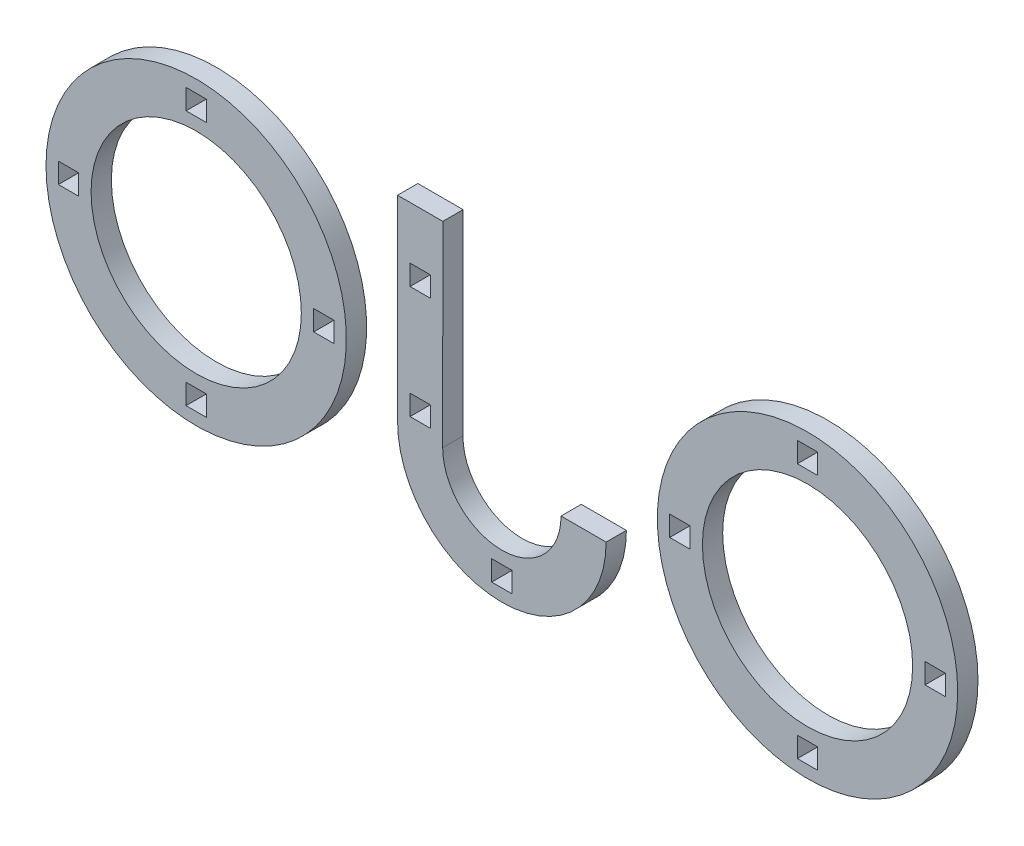
SolidWorks part; units mm, degrees
ref_plane "Ön Düzlem" through (0, 0, 0) normal (0, 0, 1) x (1, 0, 0)
ref_plane "Üst Düzlem" through (0, 0, 0) normal (0, 1, 0) x (1, 0, 0)
ref_plane "Sağ Düzlem" through (0, 0, 0) normal (1, 0, 0) x (0, 0, -1)
sketch "Sketch1" plane through (0, 0, 0) normal (0, 0, 1) x (1, 0, 0)
  line L17 (21.5127, -4.6025) -> (15.5066, -4.6025)
  line L50 (-0.2323, 21.5114) -> (-0.2534, -4.5961)
  line L51 (-6.2596, 21.5114) -> (-6.2596, -4.6025)
  line L52 (-0.2323, 21.5114) -> (-6.2596, 21.5114)
  line L53 (63.9821, 2.8614) -> (63.9821, 0.1614)
  line L54 (63.9821, 0.1614) -> (66.6821, 0.1614)
  line L59 (66.6821, 0.1614) -> (66.6821, 2.8614)
  line L60 (66.6821, 2.8614) -> (63.9821, 2.8614)
  line L61 (46.9821, 19.8614) -> (46.9821, 17.1614)
  line L62 (46.9821, 17.1614) -> (49.6821, 17.1614)
  line L63 (49.6821, 17.1614) -> (49.6821, 19.8614)
  line L64 (49.6821, 19.8614) -> (46.9821, 19.8614)
  line L65 (46.9821, -14.1386) -> (46.9821, -16.8386)
  line L66 (46.9821, -16.8386) -> (49.6821, -16.8386)
  line L67 (49.6821, -16.8386) -> (49.6821, -14.1386)
  line L68 (49.6821, -14.1386) -> (46.9821, -14.1386)
  line L69 (29.9821, 2.8614) -> (29.9821, 0.1614)
  line L70 (29.9821, 0.1614) -> (32.6821, 0.1614)
  line L71 (32.6821, 0.1614) -> (32.6821, 2.8614)
  line L72 (32.6821, 2.8614) -> (29.9821, 2.8614)
  line L73 (-17.4252, 2.8614) -> (-14.7252, 2.8614)
  line L74 (-4.5959, -0.4857) -> (-4.5959, -3.1857)
  line L75 (-17.4252, 0.1614) -> (-17.4252, 2.8614)
  line L76 (-14.7252, 0.1614) -> (-17.4252, 0.1614)
  line L77 (-14.7252, 2.8614) -> (-14.7252, 0.1614)
  line L78 (-34.4252, -14.1386) -> (-31.7252, -14.1386)
  line L79 (-34.4252, -16.8386) -> (-34.4252, -14.1386)
  line L80 (-31.7252, -16.8386) -> (-34.4252, -16.8386)
  line L81 (-31.7252, -14.1386) -> (-31.7252, -16.8386)
  line L82 (-34.4252, 19.8614) -> (-31.7252, 19.8614)
  line L83 (-34.4252, 17.1614) -> (-34.4252, 19.8614)
  line L84 (-31.7252, 17.1614) -> (-34.4252, 17.1614)
  line L85 (-31.7252, 19.8614) -> (-31.7252, 17.1614)
  line L86 (-51.4252, 2.8614) -> (-48.7252, 2.8614)
  line L87 (-51.4252, 0.1614) -> (-51.4252, 2.8614)
  line L88 (-48.7252, 0.1614) -> (-51.4252, 0.1614)
  line L89 (-48.7252, 2.8614) -> (-48.7252, 0.1614)
  line L90 (-4.5959, -3.1857) -> (-1.8959, -3.1857)
  line L91 (-4.5959, 14.5143) -> (-4.5959, 11.8143)
  line L92 (-4.5959, 11.8143) -> (-1.8959, 11.8143)
  line L93 (-1.8959, 11.8143) -> (-1.8959, 14.5143)
  line L94 (-1.8959, 14.5143) -> (-4.5959, 14.5143)
  line L95 (-1.8959, -3.1857) -> (-1.8959, -0.4857)
  line L96 (-1.8959, -0.4857) -> (-4.5959, -0.4857)
  line L98 (6.2766, -14.1355) -> (6.2766, -16.8355)
  line L100 (8.9766, -14.1355) -> (6.2766, -14.1355)
  line L101 (6.2766, -16.8355) -> (8.9766, -16.8355)
  line L102 (8.9766, -16.8355) -> (8.9766, -14.1355)
  circle A38 centre (48.3321, 1.5114) radius 14
  circle A39 centre (48.3321, 1.5114) radius 20
  arc A40 (-6.2596, -4.6025) -> (21.5127, -4.6025) centre (7.6266, -4.6025) ccw
  arc A43 (-0.2534, -4.5961) -> (15.5066, -4.6025) centre (7.6266, -4.6025) ccw
  circle A46 centre (-33.0752, 1.5114) radius 20
  circle A47 centre (-33.0752, 1.5114) radius 14
  point P0 (7.6285, 1.5114)
  point P51 (7.6266, -15.4855)
  dimension "D1" = 2
extrude "Boss-Extrude3" add sketch "Sketch1" along normal blind 2.7
